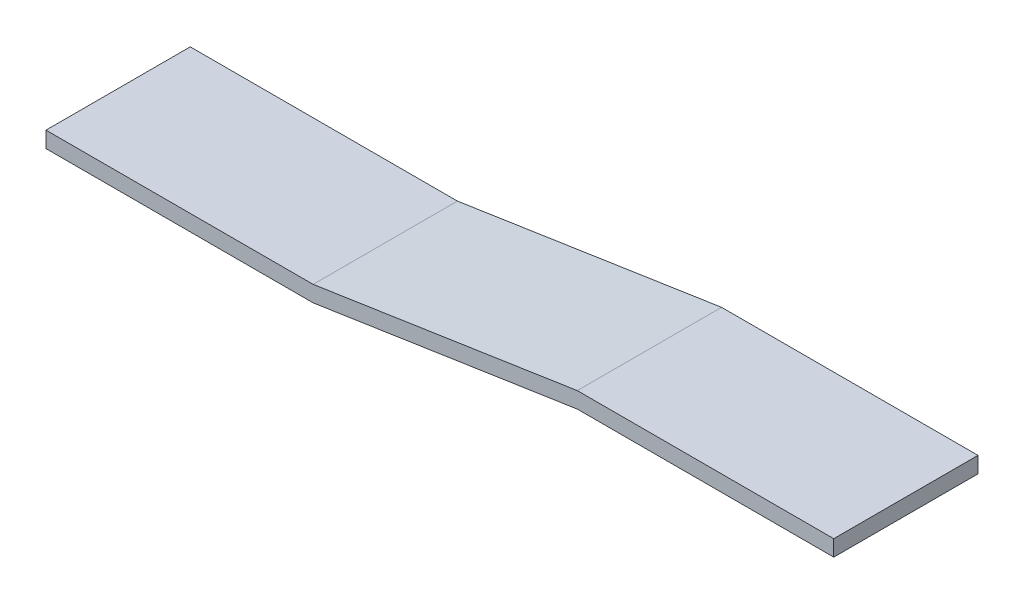
SolidWorks part; units mm, degrees
ref_plane "Plan de face" through (0, 0, 0) normal (0, 0, 1) x (1, 0, 0)
ref_plane "Plan de dessus" through (0, 0, 0) normal (0, 1, 0) x (1, 0, 0)
ref_plane "Plan de droite" through (0, 0, 0) normal (1, 0, 0) x (0, 0, -1)
sketch "Esquisse1" plane through (0, 0, 0) normal (0, 0, 1) x (1, 0, 0)
  line L0 (-24, -1.5) -> (-73.4343, -9)
  line L5 (-24, 1.5) -> (24, 1.5)
  line L6 (-24, 1.5) -> (-24, -1.5) construction
  line L7 (-24, -1.5) -> (24, -1.5)
  line L8 (24, 1.5) -> (24, -1.5)
  line L9 (-24, 1.5) -> (24, -1.5) construction
  line L10 (-24, -1.5) -> (24, 1.5) construction
  line L11 (-73.4343, -9) -> (-73.4343, -6) construction
  line L12 (-73.4343, -6) -> (-24, 1.5)
  line L13 (-73.4343, -6) -> (-123.4343, -6)
  line L14 (-123.4343, -6) -> (-123.4343, -9)
  line L15 (-123.4343, -9) -> (-73.4343, -9)
  point P0 (0, 0)
  dimension "D1" = 3
  dimension "D2" = 48
  dimension "D3" = 50
  dimension "D4" = 7.5
  dimension "D5" = 50
extrude "Boss.-Extru.1" add sketch "Esquisse1" along normal blind 27
